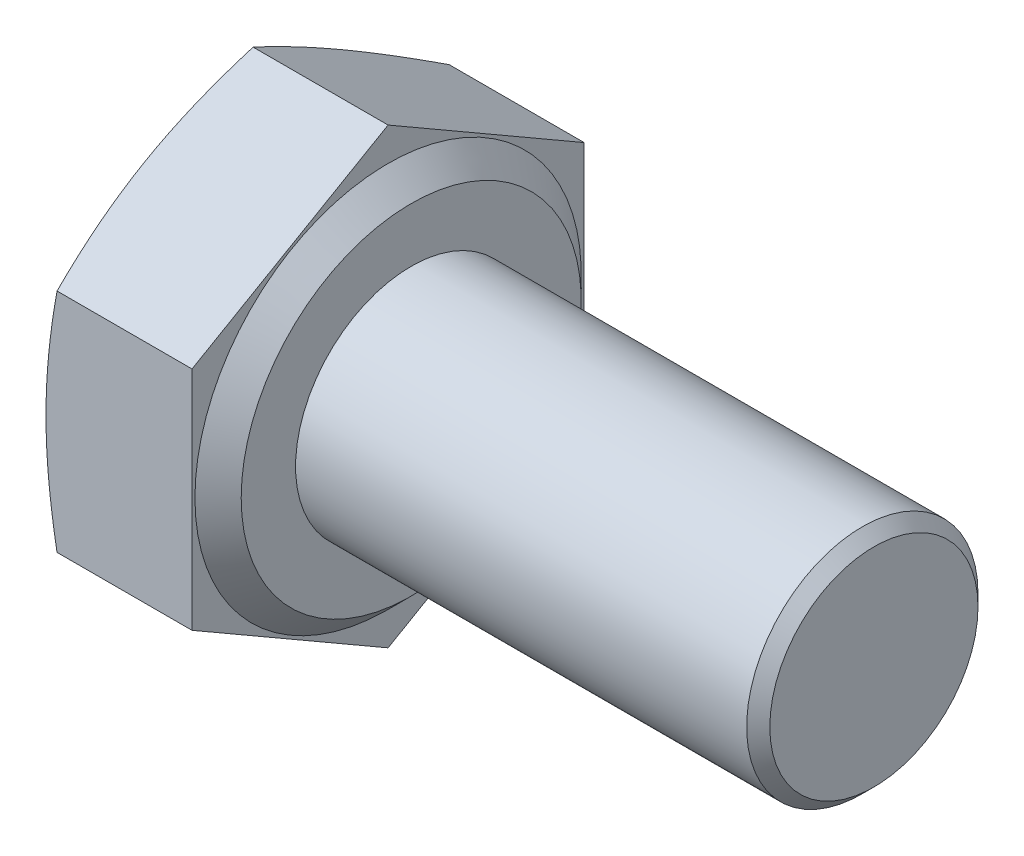
SolidWorks part; units mm, degrees
ref_plane "Front" through (0, 0, 0) normal (0, 0, 1) x (1, 0, 0)
ref_plane "Top" through (0, 0, 0) normal (0, 1, 0) x (1, 0, 0)
ref_plane "Right" through (0, 0, 0) normal (1, 0, 0) x (0, 0, -1)
sketch "Sketch2" plane through (0, 0, 0) normal (1, 0, 0) x (0, 0, -1)
  line L1 (3.39, -1.9572) -> (3.39, 1.9572)
  line L2 (3.39, 1.9572) -> (0, 3.9144)
  line L3 (0, 3.9144) -> (-3.39, 1.9572)
  line L4 (-3.39, 1.9572) -> (-3.39, -1.9572)
  line L5 (-3.39, -1.9572) -> (0, -3.9144)
  line L6 (0, -3.9144) -> (3.39, -1.9572)
  circle A0 centre (0, 0) radius 3.39 construction
  dimension "s" = 6.78
extrude "BaseHead" add sketch "Sketch2" along normal blind 2.925
sketch "Sketch3" plane through (0, 0, 0) normal (0, 0, 1) x (1, 0, 0)
  line L0 (2.925, 3.9144) -> (2.925, 2.94)
  line L2 (2.925, 2.94) -> (2.525, 3.34)
  line L3 (2.525, 3.34) -> (2.525, 3.9144)
  line L5 (2.525, 3.9144) -> (2.925, 3.9144)
  line L6 (-0.9571, 0) -> (7.6478, 0) construction
  line L7 (2.925, 3.9144) -> (0, 3.9144) construction
  dimension "D1" = 45
  dimension "c" = 0.4
  dimension "Dw" = 5.88
revolve "BearingFace" cut sketch "Sketch3" angle 360 about L6
sketch "Sketch4" plane through (0, 0, 0) normal (0, 0, 1) x (1, 0, 0)
  line L0 (-0.4935, 0) -> (3.5626, 0) construction
  line L2 (0, 3.9144) -> (0.1909, 3.9144)
  line L4 (0.1909, 3.9144) -> (0, 3.39)
  line L6 (0, 3.39) -> (0, 3.9144)
  line L7 (2.525, 3.9144) -> (0, 3.9144) construction
  dimension "D1" = 20
  dimension "D2" = 6.78
revolve "HeadChamfer" cut sketch "Sketch4" angle 360 about L0
sketch "Sketch5" plane through (2.925, 0, 0) normal (1, 0, 0) x (0, 0, -1)
  circle A0 centre (0, 0) radius 2
  dimension "d" = 4
extrude "BaseBody" add sketch "Sketch5" along normal blind 8
cosmetic thread "ThreadCosmetic1" [suppressed] parameters "D2"=3.242
chamfer "Chamfer1" distance 0.2 angle 45 1 edges at (10.925, 0, -2)
fillet "HeadFillet" [suppressed] radius 0.2
sketch "Sketch6" plane through (0, 0, 0) normal (0, 0, 1) x (1, 0, 0)
  line L0 (2.925, 2.379) -> (3.304, 2.379)
  line L1 (3.304, 2.379) -> (3.304, 2)
  line L2 (3.304, 2) -> (3.1145, 1.6718)
  line L3 (3.1145, 1.6718) -> (2.925, 2)
  line L4 (2.925, 2) -> (2.925, 2.379)
  line L5 (10.725, 2) -> (2.925, 2) construction
  line L6 (2.925, -2.94) -> (2.925, 2.94) construction
  dimension "D1" = 0.379
revolve "Cut-Revolve10" [suppressed] cut sketch "Sketch6" angle 360 about axis through (-0.9571, 0, 0) along (1, 0, 0)
pattern_linear "LPattern10" [suppressed] count 18
equation "\"D2@Sketch4\" = \"s@Sketch2\""
equation "\"D1@Chamfer1\" = 0.05 * \"d@Sketch5\""
equation "\"D1@Sketch6\" =  ( \"d@Sketch5\" - \"D2@ThreadCosmetic1\" )  / 2"
equation "\"pitch@LPattern10\" = \"D1@Sketch6\" * 1.2"
equation "\"D1@LPattern10\" = \"l@BaseBody\" / \"pitch@LPattern10\""
